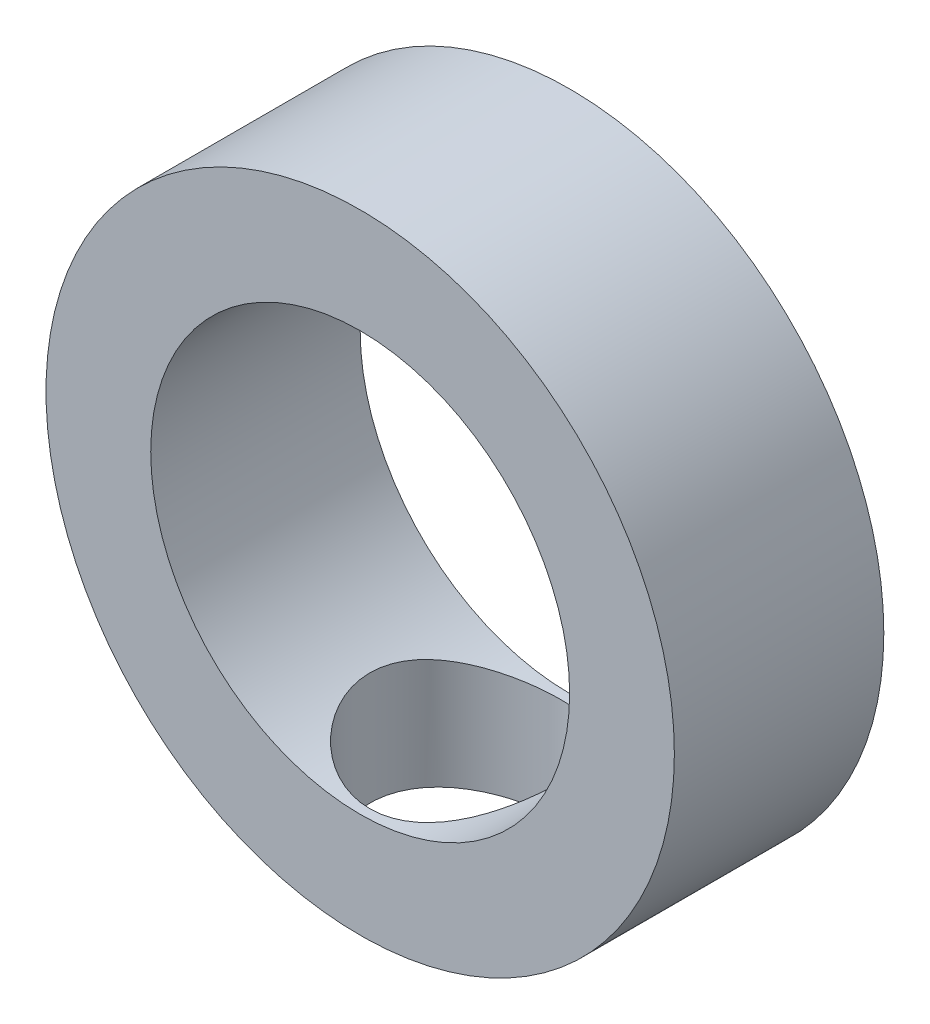
SolidWorks part; units mm, degrees
ref_plane "Front Plane" through (0, 0, 0) normal (0, 0, 1) x (1, 0, 0)
ref_plane "Top Plane" through (0, 0, 0) normal (0, 1, 0) x (1, 0, 0)
ref_plane "Right Plane" through (0, 0, 0) normal (1, 0, 0) x (0, 0, -1)
sketch "Sketch1" plane through (0, 0, 0) normal (0, 0, 1) x (1, 0, 0)
  circle A0 centre (0, 0) radius 5
  circle A1 centre (0, 0) radius 7.5
  dimension "D1" = 10
  dimension "D2" = 15
extrude "Boss-Extrude1" add sketch "Sketch1" along normal mid plane 5
sketch "Sketch4" plane through (0, 0, 0) normal (0, 1, 0) x (1, 0, 0)
  circle A0 centre (0, 0) radius 2.2681
extrude "Cut-Extrude1" cut sketch "Sketch4" against normal blind 10 contours A0
